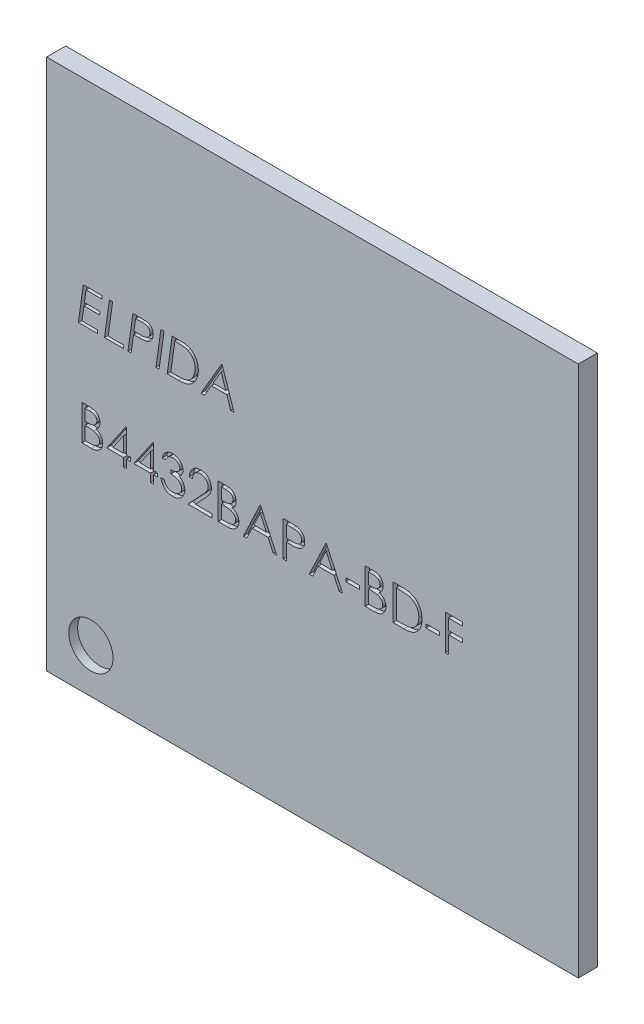
SolidWorks part; units mm, degrees
ref_plane "Plan de face" through (0, 0, 0) normal (0, 0, 1) x (1, 0, 0)
ref_plane "Plan de dessus" through (0, 0, 0) normal (0, 1, 0) x (1, 0, 0)
ref_plane "Plan de droite" through (0, 0, 0) normal (1, 0, 0) x (0, 0, -1)
sketch "Sketch1" plane through (0, 0, 0) normal (0, 0, 1) x (1, 0, 0)
  line L1 (-6, -6) -> (6, -6)
  line L2 (-6, -6) -> (-6, 6)
  line L3 (-6, 6) -> (6, 6)
  line L4 (6, -6) -> (6, 6)
  line L5 (-6, -6) -> (6, 6) construction
  line L6 (-6, 6) -> (6, -6) construction
  point P0 (0, 0)
  dimension "D1" = 12
extrude "Boss-Extrude1" add sketch "Sketch1" along normal blind 0.43
sketch "Sketch5" plane through (0, 0, 0.43) normal (0, 0, 1) x (1, 0, 0)
  line L0 (-6, -6) -> (6, -6) construction
  line L1 (-6, 6) -> (-6, -6) construction
  circle A0 centre (-5, -5) radius 0.5
  dimension "D1" = 1
  dimension "D2" = 1
  dimension "D3" = 1
extrude "Cut-Extrude2" cut sketch "Sketch5" against normal blind 0.2
sketch "Sketch4" plane through (0, 0, 0.43) normal (0, 0, 1) x (1, 0, 0)
  text T0 "<i>ELPIDA</i>\r\nB4432BAPA-BD-F" font "Century Gothic" height in points 3
extrude "Cut-Extrude1" cut sketch "Sketch4" against normal blind 0.1
